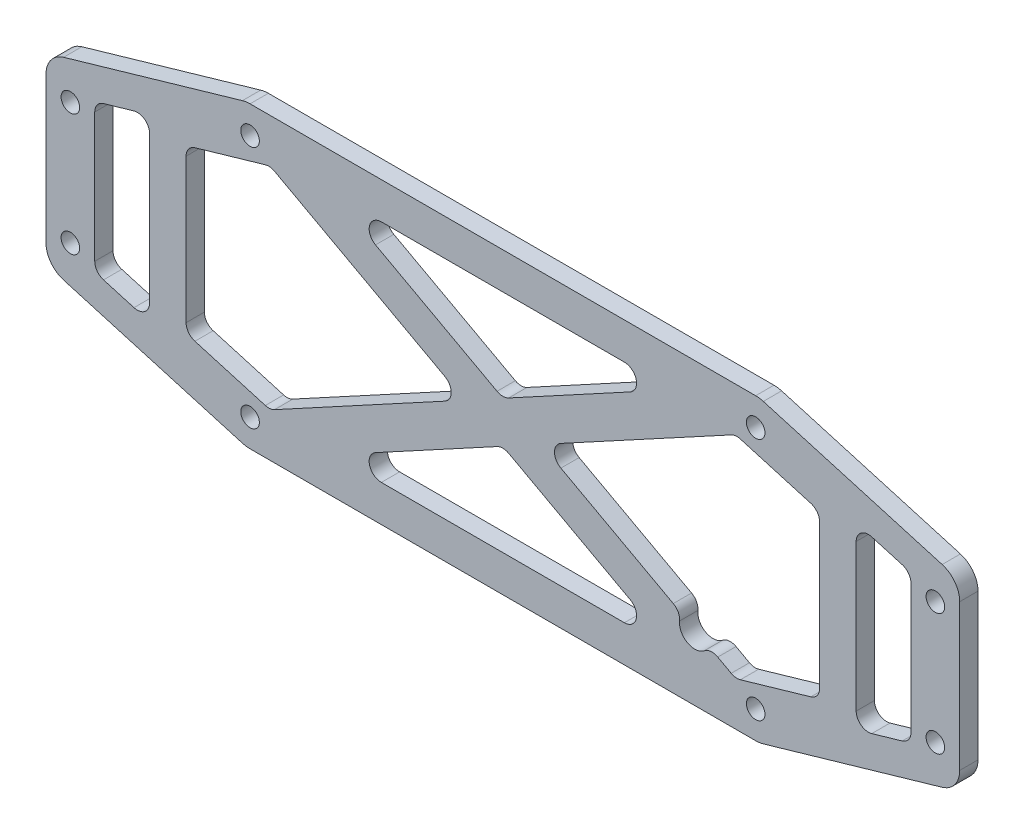
SolidWorks part; units mm, degrees
material "Thornel Mat VMA"
ref_plane "前视基准面" through (0, 0, 0) normal (0, 0, 1) x (1, 0, 0)
ref_plane "上视基准面" through (0, 0, 0) normal (0, 1, 0) x (1, 0, 0)
ref_plane "右视基准面" through (0, 0, 0) normal (1, 0, 0) x (0, 0, -1)
other "Configuration Table"
sketch "草图1" plane through (0, 0, 0) normal (0, 0, 1) x (1, 0, 0)
  line L0 (-75, 15) -> (-42.7599, 24.3461)
  line L1 (-71, -10) -> (71, -10) construction
  line L2 (-71, -10) -> (-71, 10) construction
  line L3 (-71, 10) -> (71, 10) construction
  line L4 (71, -10) -> (71, 10) construction
  line L5 (-71, -10) -> (71, 10) construction
  line L6 (-71, 10) -> (71, -10) construction
  line L7 (-75, -15) -> (75, -15)
  line L8 (-75, -15) -> (-75, 15)
  line L9 (-75, 15) -> (75, 15)
  line L10 (75, -15) -> (75, 15)
  line L11 (-75, -15) -> (75, 15) construction
  line L12 (-75, 15) -> (75, -15) construction
  line L13 (-41.5, -20) -> (41.5, -20) construction
  line L14 (-41.5, -20) -> (-41.5, 20) construction
  line L15 (-41.5, 20) -> (41.5, 20) construction
  line L16 (41.5, -20) -> (41.5, 20) construction
  line L17 (-41.5, -20) -> (41.5, 20) construction
  line L18 (-41.5, 20) -> (41.5, -20) construction
  line L19 (-41.5, 24.525) -> (41.5, 24.525)
  line L20 (75, 15) -> (42.7599, 24.3461)
  line L21 (-75, -15) -> (-42.7599, -24.3461)
  line L22 (-41.5, -24.525) -> (41.5, -24.525)
  line L23 (75, -15) -> (42.7599, -24.3461)
  circle A0 centre (-71, 10) radius 1.525
  circle A1 centre (71, 10) radius 1.525
  circle A2 centre (71, -10) radius 1.525
  circle A3 centre (-71, -10) radius 1.525
  circle A4 centre (-41.5, 20) radius 1.525
  circle A5 centre (41.5, 20) radius 1.525
  circle A6 centre (-41.5, -20) radius 1.525
  circle A7 centre (41.5, -20) radius 1.525
  circle A8 centre (-41.5, 20) radius 4.525
  circle A9 centre (41.5, 20) radius 4.525
  circle A10 centre (41.5, -20) radius 4.525
  circle A11 centre (-41.5, -20) radius 4.525
  point P0 (0, 0)
  point P6 (0, 0)
  point P15 (0, 0)
  dimension "D3" = 3.05
  dimension "D8" = 3.05
  dimension "D9" = 3
  dimension "D1" = 20
  dimension "D2" = 142
  dimension "D4" = 4
  dimension "D5" = 5
  dimension "D6" = 40
  dimension "D7" = 83
extrude "凸台-拉伸1" add sketch "草图1" along normal blind 3 contours A9 L19 A8 L0 L9 L20 | L7 L10 L9 L8 A3 A2 A1 A0 | A11 L22 A10 L23 L7 L21 | A11 A6 | A8 A4 | A9 A5 | A10 A7
fillet "圆角1" radius 4 4 edges at (75, 15, 1.5) (75, -15, 1.5) (-75, -15, 1.5) (-75, 15, 1.5)
sketch "草图2" plane through (0, 0, 3) normal (0, 0, 1) x (1, 0, 0)
  line L0 (-75, 0) -> (-55, 0) construction
  line L1 (-75, -11.9949) -> (-75, 11.9949) construction
  line L2 (-55, 0) -> (55, 0) construction
  line L3 (55, 0) -> (75, 0) construction
  line L4 (75, -11.9949) -> (75, 11.9949) construction
  line L5 (-58, 14.7223) -> (-67, 12.1133)
  line L6 (-67, 12.1133) -> (-67, -12.1133)
  line L7 (-67, -12.1133) -> (-58, -14.7223)
  line L8 (-58, -14.7223) -> (-58, 14.7223)
  line L9 (0, 0) -> (0, -50000) construction
  line L10 (-72.1137, 15.8367) -> (-42.7599, 24.3461) construction
  line L11 (-52, 13.3381) -> (-52, -13.3381)
  line L12 (-52, -13.3381) -> (-34.1073, -18.525)
  line L13 (-34.1073, -18.525) -> (34.1073, -18.525)
  line L14 (-52, 13.3381) -> (-34.1073, 18.525)
  line L15 (-34.1073, 18.525) -> (34.1073, 18.525)
  line L16 (52, -13.3381) -> (34.1073, -18.525)
  line L17 (52, 13.3381) -> (52, -13.3381)
  line L18 (52, 13.3381) -> (34.1073, 18.525)
  line L19 (67, -12.1133) -> (58, -14.7223)
  line L20 (67, 12.1133) -> (67, -12.1133)
  line L21 (58, 14.7223) -> (67, 12.1133)
  line L22 (58, -14.7223) -> (58, 14.7223)
  line L23 (-34.1073, 18.525) -> (34.1073, -18.525) construction
  line L24 (34.1073, 18.525) -> (-34.1073, -18.525) construction
  line L25 (-41.5, 24.525) -> (41.5, 24.525) construction
  line L26 (-38.2055, 17.337) -> (32.6754, -21.1612)
  line L27 (32.6754, 21.1612) -> (-38.2055, -17.337)
  line L28 (-32.6754, 21.1612) -> (38.2055, -17.337)
  line L29 (38.2055, 17.337) -> (-32.6754, -21.1612)
  line L30 (-35.5391, 15.8888) -> (32.6754, -21.1612) construction
  line L31 (35.5391, 15.8888) -> (-32.6754, -21.1612) construction
  line L32 (-32.6754, 21.1612) -> (35.5391, -15.8888) construction
  line L33 (32.6754, 21.1612) -> (-35.5391, -15.8888) construction
  circle A0 centre (-41.5, 20) radius 4.525 construction
  point P27 (-37.7488, 17.4694)
  point P29 (0, -18.525)
  point P32 (0, 18.525)
  point P36 (37.7488, -17.4694)
  point P37 (-37.7488, 17.4694)
  point P38 (-35.7453, 18.0502)
  point P49 (-38.1082, 17.3652)
  point P51 (0, 0)
  point P52 (0, 0)
  point P53 (38.2055, 17.337)
  point P55 (38.2055, -17.337)
  point P58 (-38.2055, -17.337)
  dimension "D1" = 20
  dimension "D2" = 8
  dimension "D3" = 5
  dimension "D4" = 3
  dimension "D5" = 8
  dimension "D6" = 6
  dimension "D7" = 6
  dimension "D8" = 3
  dimension "D9" = 3
extrude "切除-拉伸1" cut sketch "草图2" against normal blind 10 contours L15 L28 L27 | L27 L26 L14 L11 L12 | L26 L29 L13 | L18 L29 L28 L16 L17 | L22 L19 L20 L21 | L7 L8 L5 L6
fillet "圆角2" radius 2 24 edges at (27.8217, -18.525, 1.5) (-27.8217, -18.525, 1.5) (0, -3.4139, 1.5) (58, 14.7223, 1.5) (67, 12.1133, 1.5) (67, -12.1133, 1.5) (58, -14.7223, 1.5) (27.8217, 18.525, 1.5) (0, 3.4139, 1.5) (-27.8217, 18.525, 1.5) (52, -13.3381, 1.5) (38.2055, -17.337, 1.5) (6.2856, 0, 1.5) (38.2055, 17.337, 1.5) (52, 13.3381, 1.5) (-38.2055, -17.337, 1.5) (-52, -13.3381, 1.5) (-52, 13.3381, 1.5) (-38.2055, 17.337, 1.5) (-6.2856, 0, 1.5) (-58, 14.7223, 1.5) (-58, -14.7223, 1.5) (-67, -12.1133, 1.5) (-67, 12.1133, 1.5)
sketch "草图4" plane through (0, 0, 0) normal (0, 0, -1) x (-1, 0, 0)
  circle A0 centre (-31.5, -14) radius 2.5
  dimension "D1" = 5
extrude "切除-拉伸2" cut sketch "草图4" against normal blind 10
fillet "圆角3" radius 2 2 edges at (33.8122, -14.9508, 1.5) (29.4437, -12.5781, 1.5)
